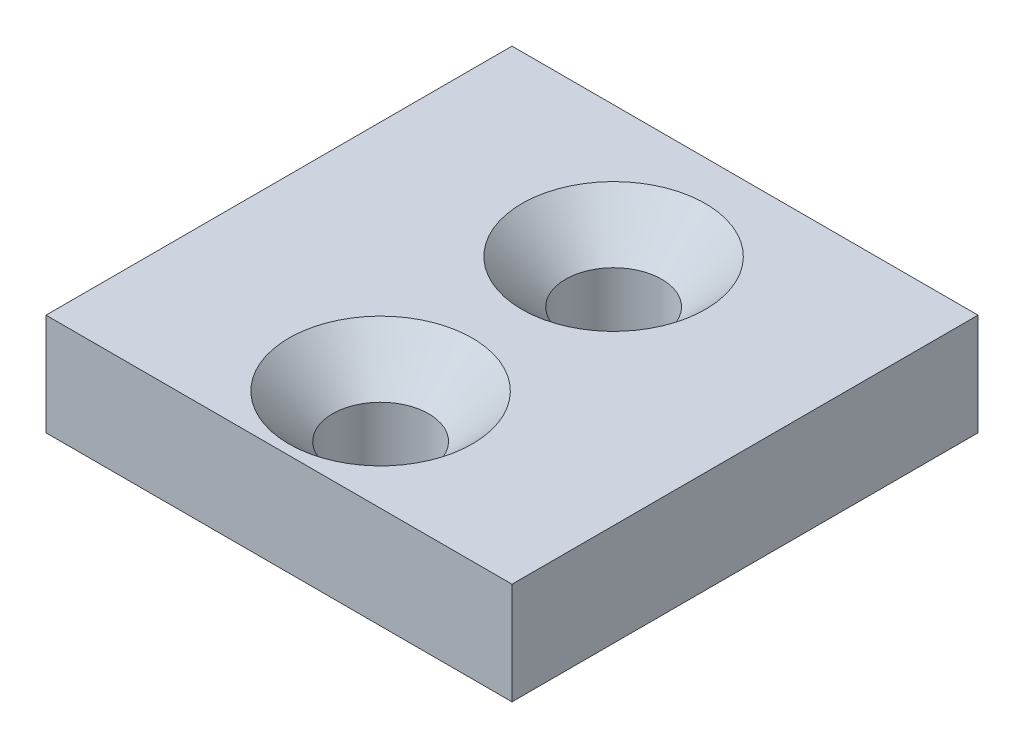
SolidWorks part; units mm, degrees
ref_plane "Ön Düzlem" through (0, 0, 0) normal (0, 0, 1) x (1, 0, 0)
ref_plane "Üst Düzlem" through (0, 0, 0) normal (0, 1, 0) x (1, 0, 0)
ref_plane "Sağ Düzlem" through (0, 0, 0) normal (1, 0, 0) x (0, 0, -1)
sketch "Çizim1" plane through (0, 0, 0) normal (0, 1, 0) x (1, 0, 0)
  line L1 (0, 0) -> (-32, 0)
  line L2 (0, 0) -> (0, 32)
  line L3 (0, 32) -> (-32, 32)
  line L4 (-32, 0) -> (-32, 32)
  dimension "D1" = 32
  dimension "D2" = 32
extrude "Yükseklik-Ekstrüzyon1" add sketch "Çizim1" along normal blind 7
hole_wizard "Delik2" positions "Çizim13" profile "Çizim14" legacy
sketch "Çizim13" plane through (0, 7, 0) normal (0, 1, 0) x (1, 0, 0)
  point P8 (-16, 22.9771)
  point P10 (-16, 6.9771)
  dimension "D1" = 16
sketch "Çizim14" plane through (-16, 7, -22.9771) normal (1, 0, 0) x (0, 0, 1)
  line L0 (0, 0) -> (0, 6.999)
  line L1 (0, 6.999) -> (3.3, 6.999)
  line L2 (3.3, 6.999) -> (3.3, 3)
  line L3 (3.3, 3) -> (6.3, 0)
  line L4 (6.3, 0) -> (0, 0)
  line L5 (0, -6.4453) -> (0, 115.525) construction
  line L6 (-3.3, 3) -> (-6.3, 0) construction
  dimension "Diameter" = 6.6
  dimension "Depth" = 6.999
  dimension "C-Sink Angle" = 90
  dimension "C-Sink Diameter" = 12.6
